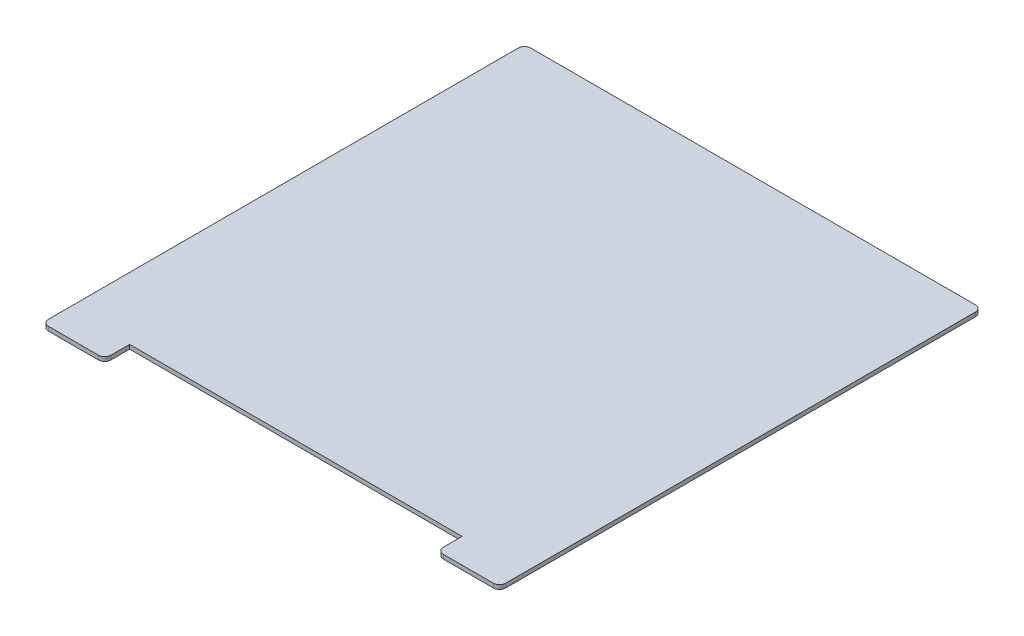
SolidWorks part; units mm, degrees
ref_plane "Front Plane" through (0, 0, 0) normal (0, 0, 1) x (1, 0, 0)
ref_plane "Top Plane" through (0, 0, 0) normal (0, 1, 0) x (1, 0, 0)
ref_plane "Right Plane" through (0, 0, 0) normal (1, 0, 0) x (0, 0, -1)
sketch "Sketch1" plane through (0, 0, 0) normal (0, 1, 0) x (1, 0, 0)
  line L0 (-160, -197.6497) -> (-160, -185.6497)
  line L1 (-190, 34.3503) -> (30, 34.3503)
  line L2 (-190, 34.3503) -> (-190, -197.6497)
  line L3 (-190, -197.6497) -> (-160, -197.6497)
  line L4 (30, 34.3503) -> (30, -197.6497)
  line L5 (-160, -185.6497) -> (0, -185.6497)
  line L6 (0, -185.6497) -> (0, -197.6497)
  line L7 (0, -197.6497) -> (30, -197.6497)
  dimension "D1" = 220
  dimension "D2" = 12
  dimension "D3" = 220
  dimension "D4" = 30
  dimension "D5" = 30
extrude "Boss-Extrude1" add sketch "Sketch1" along normal blind 2
fillet "Fillet1" radius 3 6 edges at (30, 1, -34.3503) (-190, 1, -34.3503) (-160, 1, 197.6497) (-190, 1, 197.6497) (30, 1, 197.6497) (0, 1, 197.6497)
